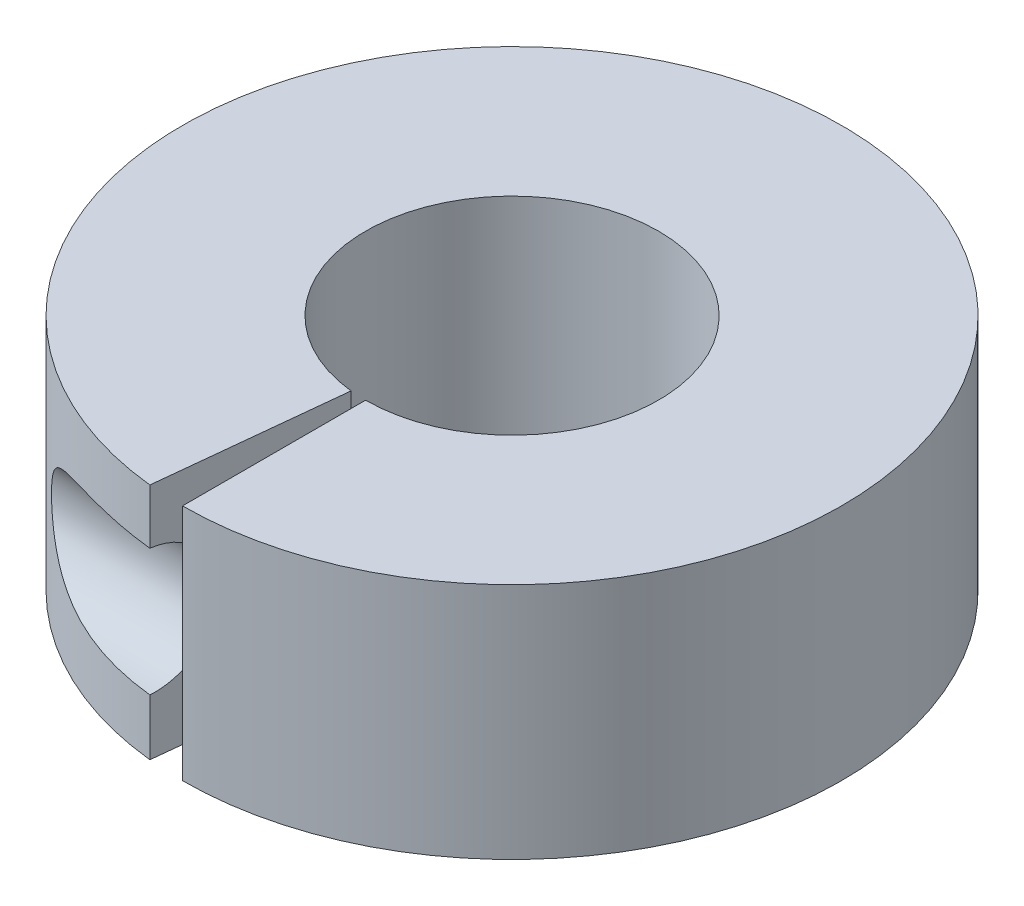
SolidWorks part; units mm, degrees
ref_plane "Front Plane" through (0, 0, 0) normal (0, 0, 1) x (1, 0, 0)
ref_plane "Top Plane" through (0, 0, 0) normal (0, 1, 0) x (1, 0, 0)
ref_plane "Right Plane" through (0, 0, 0) normal (1, 0, 0) x (0, 0, -1)
sketch "Sketch1" plane through (0, 0, 0) normal (0, 1, 0) x (1, 0, 0)
  circle A0 centre (0, 0) radius 6.35
  circle A1 centre (0, 0) radius 14.2875
  dimension "D1" = 12.7
  dimension "D2" = 28.575
extrude "Boss-Extrude1" add sketch "Sketch1" along normal blind 10.3187
sketch "Sketch2" plane through (0, 0, 0) normal (1, 0, 0) x (0, 0, -1)
  line L0 (-14.2875, 10.3187) -> (-14.2875, 0) construction
  line L1 (-14.2875, 7.9444) -> (-16.0712, 7.9444)
  line L2 (-16.0712, 7.9444) -> (-16.0712, 2.4352)
  line L3 (-16.0712, 2.4352) -> (-14.2875, 2.4352)
  arc A0 (-14.2875, 7.9444) -> (-14.2875, 2.4352) centre (-14.2875, 5.1898) cw
extrude "Cut-Extrude1" cut sketch "Sketch2" against normal blind 10.3187
sketch "Sketch3" plane through (0, 10.3187, 0) normal (0, 1, 0) x (1, 0, 0)
  line L0 (0, 0) -> (0, -14.2875) construction
  line L1 (0, -6.35) -> (0, -14.2875)
  line L2 (-0.6638, -6.3152) -> (-1.4935, -14.2092)
  circle A0 centre (0, 0) radius 14.2875 construction
  circle A1 centre (0, 0) radius 6.35 construction
  arc A2 (-0.6638, -6.3152) -> (0, -6.35) centre (0, 0) ccw
  arc A3 (-1.4935, -14.2092) -> (0, -14.2875) centre (0, 0) ccw
  dimension "D1" = 6
extrude "Cut-Extrude2" cut sketch "Sketch3" against normal blind 10.3187
